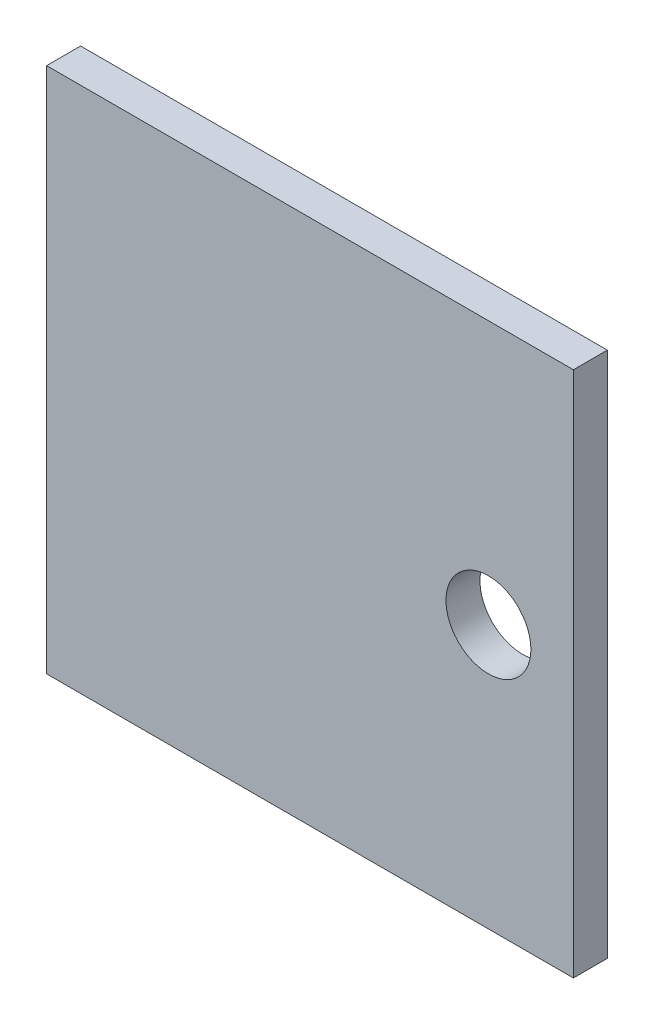
SolidWorks part; units mm, degrees
ref_plane "Front Plane" through (0, 0, 0) normal (0, 0, 1) x (1, 0, 0)
ref_plane "Top Plane" through (0, 0, 0) normal (0, 1, 0) x (1, 0, 0)
ref_plane "Right Plane" through (0, 0, 0) normal (1, 0, 0) x (0, 0, -1)
sketch "Sketch1" plane through (0, 0, 0) normal (0, 0, 1) x (1, 0, 0)
  line L0 (79.971, 0) -> (0, 0) construction
  line L1 (0, 0) -> (-78.5333, 0) construction
  line L2 (0, 58.4957) -> (0, 0) construction
  line L3 (0, 0) -> (0, -56.6986) construction
  line L5 (-31, 31) -> (31, 31)
  line L6 (-31, 31) -> (-31, -31)
  line L7 (-31, -31) -> (31, -31)
  line L8 (31, 31) -> (31, -31)
  line L9 (-31, 31) -> (31, -31) construction
  line L10 (-31, -31) -> (31, 31) construction
  circle A0 centre (21, 0) radius 5
  dimension "D3" = 10
  dimension "D1" = 62
  dimension "D2" = 62
  dimension "D4" = 10
extrude "Boss-Extrude1" add sketch "Sketch1" along normal blind 4
